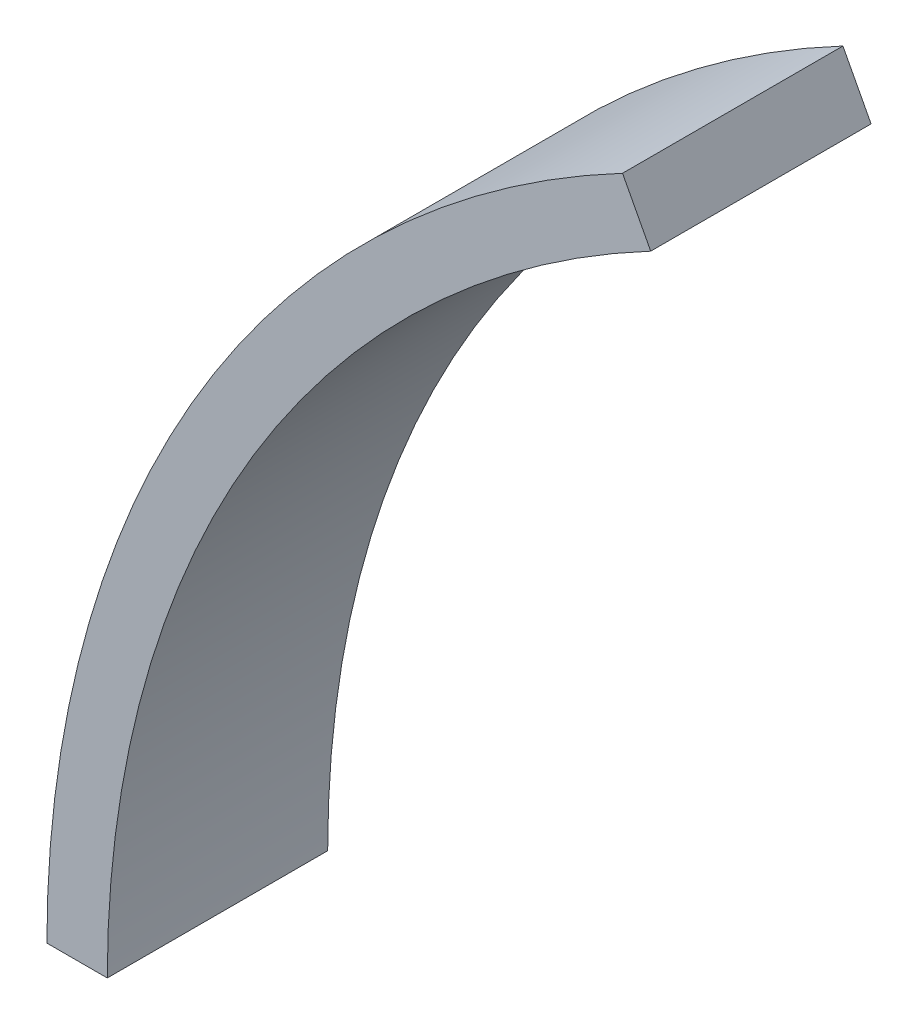
SolidWorks part; units mm, degrees
ref_plane "Front Plane" through (0, 0, 0) normal (0, 0, 1) x (1, 0, 0)
ref_plane "Top Plane" through (0, 0, 0) normal (0, 1, 0) x (1, 0, 0)
ref_plane "Right Plane" through (0, 0, 0) normal (1, 0, 0) x (0, 0, -1)
sketch "Sketch1" plane through (0, 0, 0) normal (0, 0, 1) x (1, 0, 0)
  line L0 (-20.0025, 37.909) -> (-20.0025, 83.5446) construction
  line L1 (20.0025, 37.909) -> (20.0025, 83.5446) construction
  line L2 (0, 0) -> (-42.8625, 0) construction
  line L3 (-42.8625, 0) -> (-45.4025, 0)
  line L4 (-20.0025, 37.909) -> (-21.1878, 40.1555)
  circle A0 centre (0, 0) radius 42.8625 construction
  arc A1 (-42.8625, 0) -> (-20.0025, 37.909) centre (0, 0) cw
  arc A2 (-45.4025, 0) -> (-21.1878, 40.1555) centre (0, 0) cw
  dimension "D1" = 85.725
  dimension "D2" = 40.005
  dimension "D3" = 2.54
extrude "Boss-Extrude1" add sketch "Sketch1" along normal mid plane 9.271
